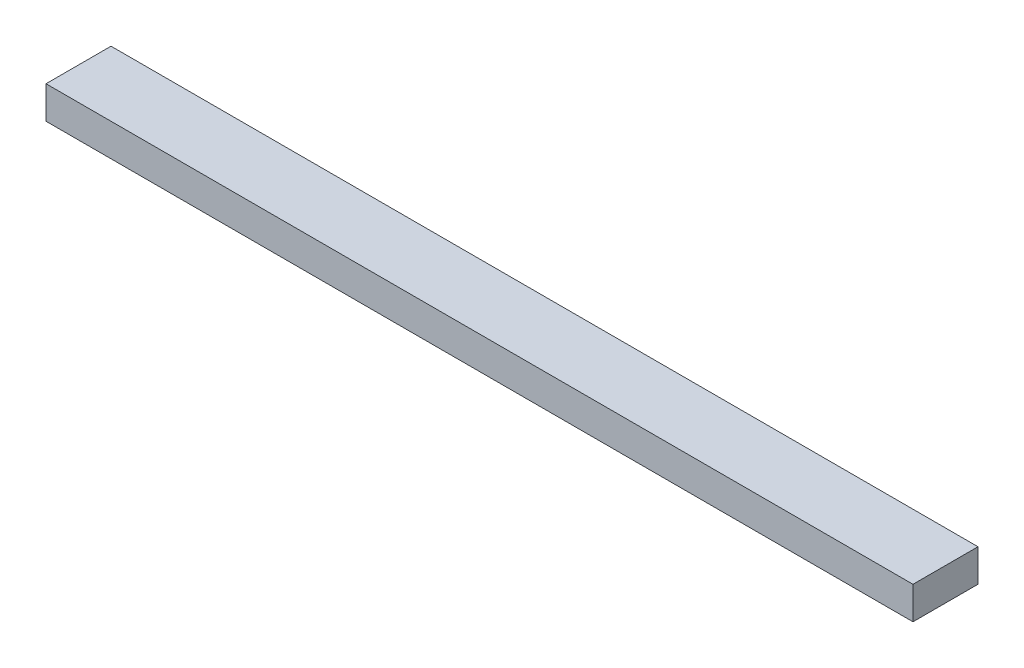
SolidWorks part; units mm, degrees
material "Pine"
ref_plane "Front Plane" through (0, 0, 0) normal (0, 0, 1) x (1, 0, 0)
ref_plane "Top Plane" through (0, 0, 0) normal (0, 1, 0) x (1, 0, 0)
ref_plane "Right Plane" through (0, 0, 0) normal (1, 0, 0) x (0, 0, -1)
sketch "Sketch1" plane through (0, 0, 0) normal (0, 1, 0) x (1, 0, 0)
  line L1 (0, 0) -> (508, 0)
  line L2 (0, 0) -> (0, 38.1)
  line L3 (0, 38.1) -> (508, 38.1)
  line L4 (508, 0) -> (508, 38.1)
  dimension "D1" = 38.1
  dimension "D2" = 508
extrude "Boss-Extrude1" add sketch "Sketch1" along normal blind 19.05
